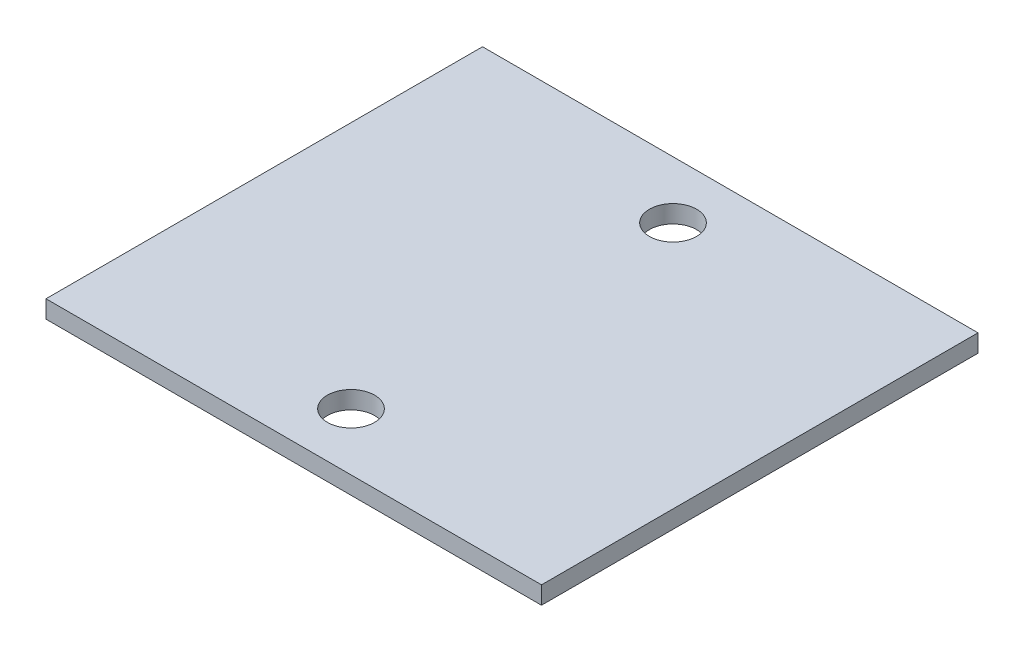
SolidWorks part; units mm, degrees
ref_plane "Спереди" through (0, 0, 0) normal (0, 0, 1) x (1, 0, 0)
ref_plane "Сверху" through (0, 0, 0) normal (0, 1, 0) x (1, 0, 0)
ref_plane "Справа" through (0, 0, 0) normal (1, 0, 0) x (0, 0, -1)
sketch "Эскиз1" plane through (0, 0, 0) normal (0, 1, 0) x (1, 0, 0)
  line L0 (21, 38.3749) -> (21, -2.9839) construction
  line L1 (0, 0) -> (42, 0)
  line L2 (0, 0) -> (0, 37)
  line L3 (0, 37) -> (42, 37)
  line L4 (42, 0) -> (42, 37)
  line L5 (0, 18.5) -> (42, 18.5) construction
  circle A0 centre (21, 32.1488) radius 2
  circle A1 centre (21, 4.8512) radius 2
  point P13 (0, 0)
  point P14 (21.5, 38.3749)
  point P15 (21, 0)
  point P16 (0, 0)
  point P17 (0, 0)
  point P18 (0, 0)
  point P19 (0, 0)
extrude "Бобышка-Вытянуть1" add sketch "Эскиз1" along normal blind 1.5
